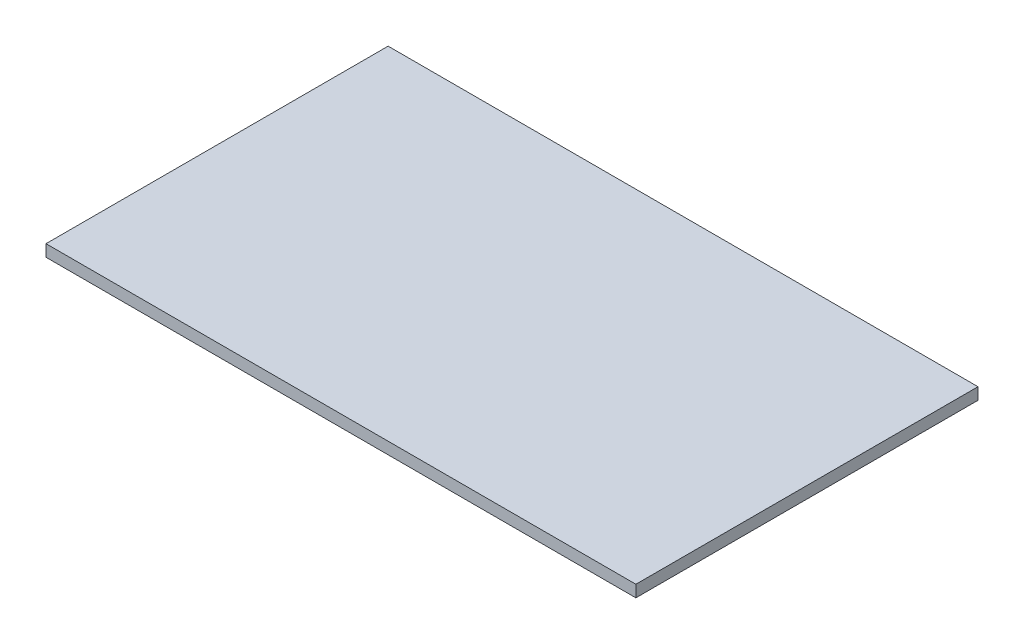
SolidWorks part; units mm, degrees
ref_plane "Front Plane" through (0, 0, 0) normal (0, 0, 1) x (1, 0, 0)
ref_plane "Top Plane" through (0, 0, 0) normal (0, 1, 0) x (1, 0, 0)
ref_plane "Right Plane" through (0, 0, 0) normal (1, 0, 0) x (0, 0, -1)
sketch "Sketch1" plane through (0, 0, 0) normal (0, 1, 0) x (1, 0, 0)
  line L1 (-250, -145) -> (250, -145)
  line L2 (-250, -145) -> (-250, 145)
  line L3 (-250, 145) -> (250, 145)
  line L4 (250, -145) -> (250, 145)
  line L5 (-250, -145) -> (250, 145) construction
  line L6 (-250, 145) -> (250, -145) construction
  point P0 (0, 0)
  dimension "D1" = 290
  dimension "D2" = 500
extrude "Boss-Extrude1" add sketch "Sketch1" along normal blind 10
